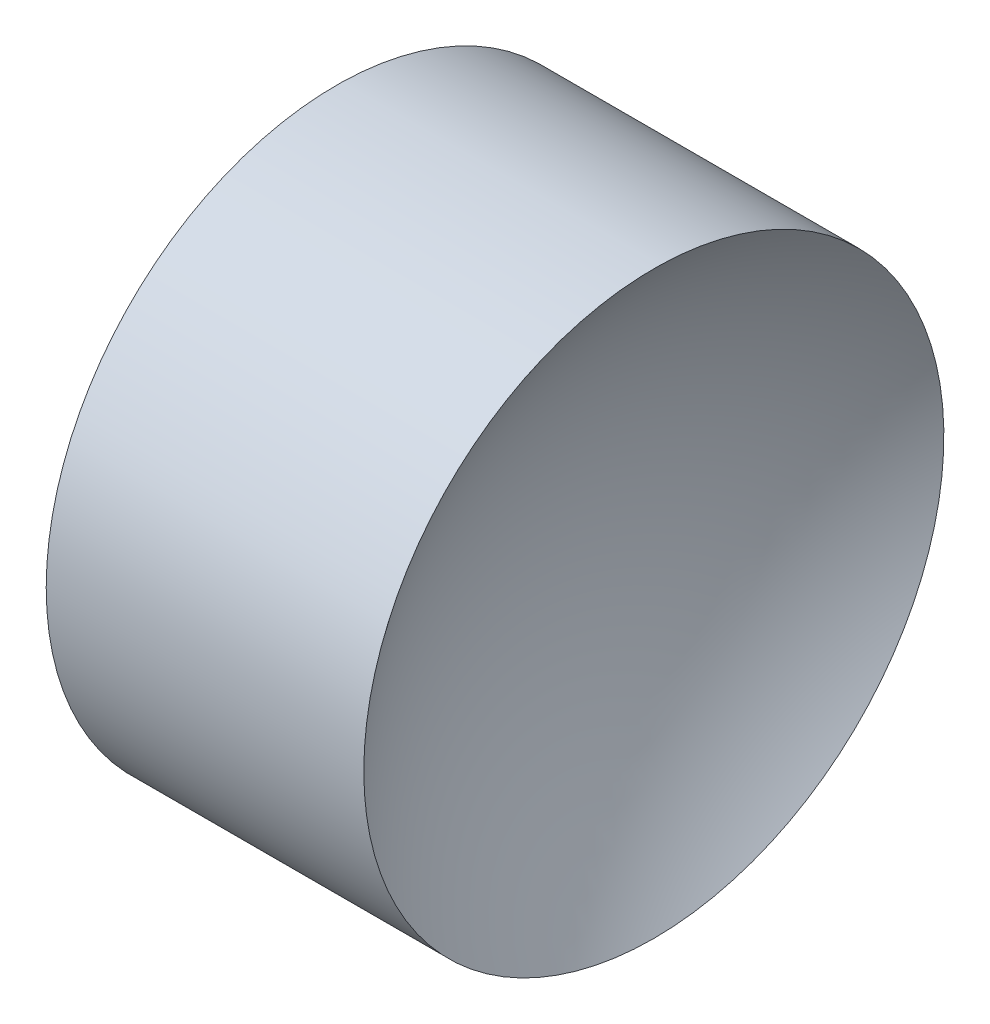
SolidWorks part; units mm, degrees
ref_plane "前视基准面" through (0, 0, 0) normal (0, 0, 1) x (1, 0, 0)
ref_plane "上视基准面" through (0, 0, 0) normal (0, 1, 0) x (1, 0, 0)
ref_plane "右视基准面" through (0, 0, 0) normal (1, 0, 0) x (0, 0, -1)
sketch "草图1" plane through (0, 0, 0) normal (0, 0, 1) x (1, 0, 0)
  line L0 (10.6125, 6.5223) -> (13.346, 6.5223) construction
  line L1 (11.0829, 6.5223) -> (11.0829, 8.5223)
  line L2 (12.5829, 6.5223) -> (11.0829, 6.5223)
  line L3 (11.0829, 8.5223) -> (13.2729, 8.5223)
  arc A0 (13.2729, 8.5223) -> (12.5829, 6.5223) centre (15.8264, 6.5223) ccw
revolve "旋转1" add sketch "草图1" angle 360 about L0
